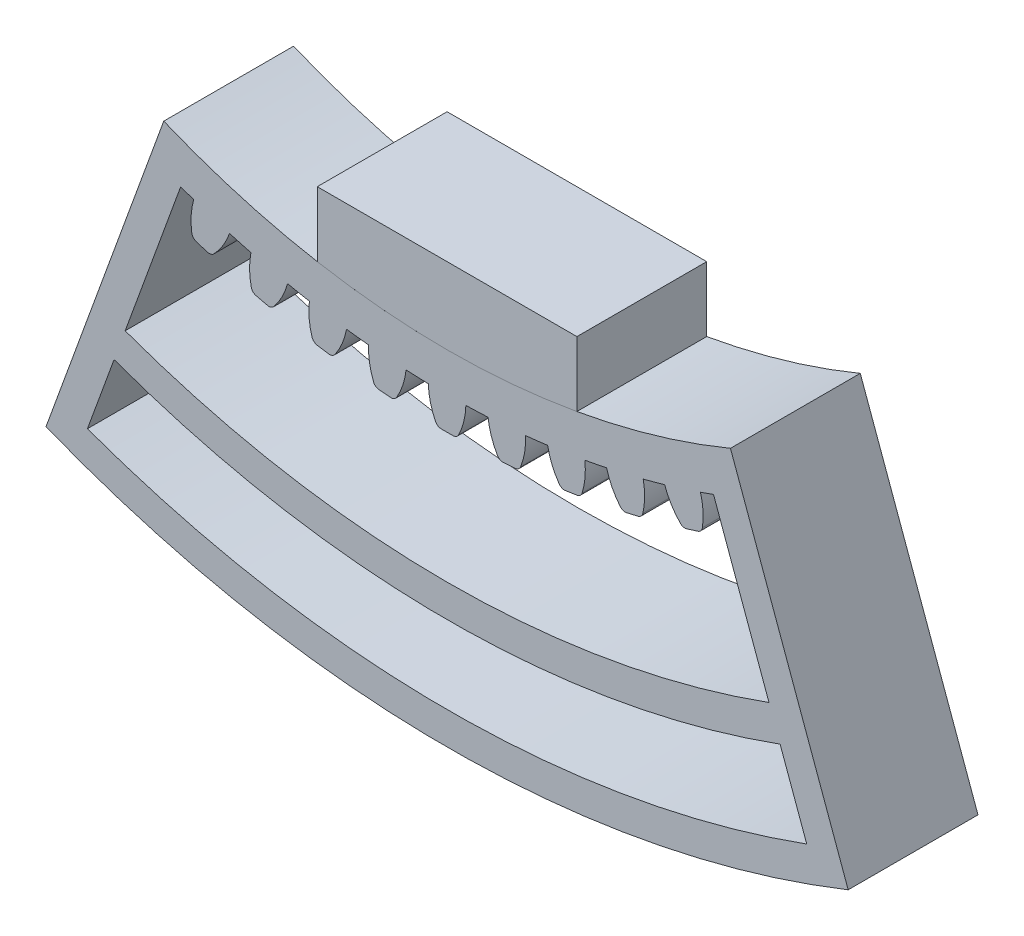
SolidWorks part; units mm, degrees
ref_plane "Plan de face" through (0, 0, 0) normal (0, 0, 1) x (1, 0, 0)
ref_plane "Plan de dessus" through (0, 0, 0) normal (0, 1, 0) x (1, 0, 0)
ref_plane "Plan de droite" through (0, 0, 0) normal (1, 0, 0) x (0, 0, -1)
sketch "Esquisse1" plane through (0, 0, 0) normal (0, 0, 1) x (1, 0, 0)
  line L0 (-49.5929, -136.2554) -> (-41.0424, -112.7631)
  line L1 (41.0424, -112.7631) -> (49.5929, -136.2554)
  line L2 (0, 0) -> (0, -167) construction
  line L3 (-83.5, -144.6262) -> (-57, -98.7269)
  line L4 (57, -98.7269) -> (83.5, -144.6262)
  line L5 (51.303, -140.9539) -> (55.4073, -152.2302)
  line L6 (-51.303, -140.9539) -> (-55.4073, -152.2302)
  arc A0 (-83.5, -144.6262) -> (83.5, -144.6262) centre (0, 0) ccw
  arc A1 (-57, -98.7269) -> (57, -98.7269) centre (0, 0) ccw
  arc A2 (-41.0424, -112.7631) -> (41.0424, -112.7631) centre (0, 0) ccw
  arc A3 (-49.5929, -136.2554) -> (49.5929, -136.2554) centre (0, 0) ccw
  arc A4 (-55.4073, -152.2302) -> (55.4073, -152.2302) centre (0, 0) ccw
  arc A5 (-51.303, -140.9539) -> (51.303, -140.9539) centre (0, 0) ccw
  point P21 (59.0684, -126.6805)
  point P22 (39.0111, -128.9523)
  dimension "D1" = 120
  dimension "D2" = 6
  dimension "D4" = 5
  dimension "D5" = 25
  dimension "D7" = 12
  dimension "D8" = 5
  dimension "D9" = 167
  dimension "D3" = 40
  dimension "D6" = 10
extrude "Boss.-Extru.1" add sketch "Esquisse1" along normal mid plane 20
sketch "Esquisse2" plane through (0, 0, 10) normal (0, 0, 1) x (1, 0, 0)
  line L0 (0, -167) -> (0, -120) construction
  circle A0 centre (0, 0) radius 120 construction
  arc A1 (-83.5, -144.6262) -> (83.5, -144.6262) centre (0, 0) ccw construction
  arc A2 (-41.0424, -112.7631) -> (41.0424, -112.7631) centre (0, 0) ccw construction
  circle A3 centre (0, 0) radius 125 construction
  arc A4 (-2.8956, -119.9651) -> (-1.5, -124.991) centre (8.099, -119.6189) ccw
  arc A5 (2.8956, -119.9651) -> (1.5, -124.991) centre (-8.099, -119.6189) cw
  arc A6 (-1.5, -124.991) -> (1.5, -124.991) centre (0, 0) ccw
  arc A7 (-2.8956, -119.9651) -> (2.8956, -119.9651) centre (0, 0) ccw
  point P0 (0, -125)
  point P19 (-2.5, -122.5619)
  point P20 (2.5, -122.5619)
  dimension "D3" = 3
  dimension "D1" = 5
  dimension "D2" = 5
  dimension "D4" = 11
extrude "Boss.-Extru.3" add sketch "Esquisse2" against normal blind 20
fillet "Congé2" radius 1 2 edges at (1.5, -124.991, 0) (-1.5, -124.991, 0)
pattern_circular "Répétition circulaire11" count 5 every 4.4 about axis through (0, 0, 0) along (0, 0, 1) of "Congé2", "Boss.-Extru.3"
sketch "Esquisse3" plane through (0, 0, 10) normal (0, 0, 1) x (1, 0, 0)
  line L0 (0, -167) -> (0, -78.7484) construction
  line L1 (-20, -112.2319) -> (20, -112.2319)
  line L2 (-20, -112.2319) -> (-20, -102.2319)
  line L3 (-20, -102.2319) -> (20, -102.2319)
  line L4 (20, -112.2319) -> (20, -102.2319)
  arc A0 (-57, -98.7269) -> (57, -98.7269) centre (0, 0) ccw construction
  arc A1 (-83.5, -144.6262) -> (83.5, -144.6262) centre (0, 0) ccw construction
  arc A2 (-20, -112.2319) -> (20, -112.2319) centre (0, 0) ccw
  arc M11 (57, -98.7269) -> (-57, -98.7269) centre (0, 0) cw
  dimension "D1" = 40
  dimension "D2" = 10
pattern_circular "Répétition circulaire12" count 5 every 4.4 about axis through (0, 0, 0) along (0, 0, 1) of "Boss.-Extru.3", "Congé2"
extrude "Boss.-Extru.5" add sketch "Esquisse3" against normal blind 20 separate body contours L1 L0 L3 L2 | L0 L1 L4 L3 | A2 L0 L1 | L0 L1 M11
sketch "Esquisse4" plane through (0, 0, -10) normal (0, 0, -1) x (-1, 0, 0)
  line L0 (43.6512, -105.3118) -> (61.7902, -155.1482)
  line L1 (41.0424, -112.7631) -> (49.5929, -136.2554) construction
  line L2 (83.5, -144.6262) -> (57, -98.7269)
  arc A0 (-57, -98.7269) -> (57, -98.7269) centre (0, 0) ccw construction
  arc A1 (-83.5, -144.6262) -> (83.5, -144.6262) centre (0, 0) ccw construction
  arc A2 (57, -98.7269) -> (43.6512, -105.3118) centre (0, 0) cw
  arc A3 (61.7902, -155.1482) -> (83.5, -144.6262) centre (0, 0) ccw
  dimension "D1" = 5
extrude "Enlèv. mat.-Extru.1" cut sketch "Esquisse4" against normal through all
mirror "Symétrie1" about plane through (0, 0, 0) normal (1, 0, 0) of "Enlèv. mat.-Extru.1"
sketch "Esquisse5" plane through (0, 0, -10) normal (0, 0, -1) x (-1, 0, 0)
  line L0 (0, -120) -> (0, -145) construction
  line L1 (0, -150) -> (0, -162) construction
  line L2 (-55.4073, -152.2302) -> (-51.303, -140.9539) construction
  line L3 (51.303, -140.9539) -> (55.4073, -152.2302) construction
  arc A2 (-41.0424, -112.7631) -> (41.0424, -112.7631) centre (0, 0) ccw construction
  arc A3 (-6.3166, -119.8336) -> (-2.8956, -119.9651) centre (0, 0) ccw construction
  arc A4 (-49.5929, -136.2554) -> (49.5929, -136.2554) centre (0, 0) ccw construction
  arc A5 (-51.303, -140.9539) -> (51.303, -140.9539) centre (0, 0) ccw construction
  arc A6 (-55.4073, -152.2302) -> (55.4073, -152.2302) centre (0, 0) ccw construction
  arc A7 (-53.3551, -146.592) -> (53.3551, -146.592) centre (0, 0) ccw construction
  point P5 (0, -132.5)
  point P22 (0, -156)
  dimension "D1" = 23.5
  dimension "D2" = 156
equation "\"4..50deg\"=4"
